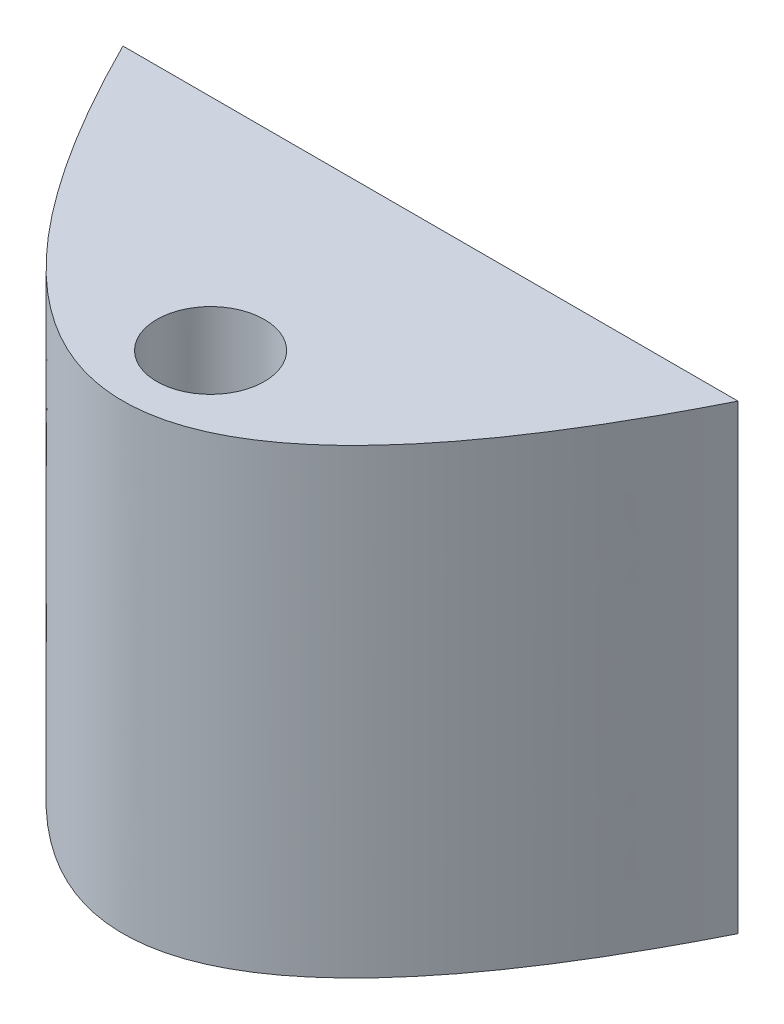
SolidWorks part; units mm, degrees
material "Custom Plastic (2)"
ref_plane "Front Plane" through (0, 0, 0) normal (0, 0, 1) x (1, 0, 0)
ref_plane "Top Plane" through (0, 0, 0) normal (0, 1, 0) x (1, 0, 0)
ref_plane "Right Plane" through (0, 0, 0) normal (1, 0, 0) x (0, 0, -1)
sketch "Sketch1" plane through (0, 0, 0) normal (0, 1, 0) x (1, 0, 0)
  line L0 (-200, 0) -> (200, 0)
  spline S0 degree 2 poles (-225.2396, 53.6645) (0, -453.6645) (225.2396, 53.6645) knots 0 0 0 1 1 1 construction
  spline S1 degree 2 poles (-200, 0) (0, -400) (200, 0) knots 0.056028 0.056028 0.056028 0.943972 0.943972 0.943972
extrude "Boss-Extrude1" add sketch "Sketch1" along normal blind 300
sketch "Sketch2" plane through (0, 300, 0) normal (0, 1, 0) x (1, 0, 0)
  line L0 (0, 200) -> (0, -200)
  line L2 (200, 0) -> (-200, 0) construction
  circle A0 centre (0, -143) radius 35
  parabola Q0 (-200, 0) -> (200, 0) focus (0, -150) apex (0, -200) construction
  point P4 (0, 0)
  dimension "D1" = 70
  dimension "D2" = 143
ref_plane "Plane1" through (0, 150, 0) normal (0, 1, 0) x (1, 0, 0)
sketch "Sketch3" plane through (0, 150, 0) normal (0, 1, 0) x (1, 0, 0)
  circle A0 centre (0, -143) radius 15.5
  dimension "D1" = 31
extrude "Cut-Extrude1" cut sketch "Sketch3" against normal blind 23 and the other way blind 23
ref_plane "Plane2" through (0, 173, 0) normal (0, 1, 0) x (1, 0, 0)
sketch "Sketch4" plane through (0, 173, 0) normal (0, 1, 0) x (1, 0, 0)
  circle A0 centre (0, -143) radius 35
extrude "Cut-Extrude3" cut sketch "Sketch4" along normal blind 300 contours A0
mirror "Mirror1" about plane through (0, 150, 0) normal (0, 1, 0) of "Cut-Extrude3"
